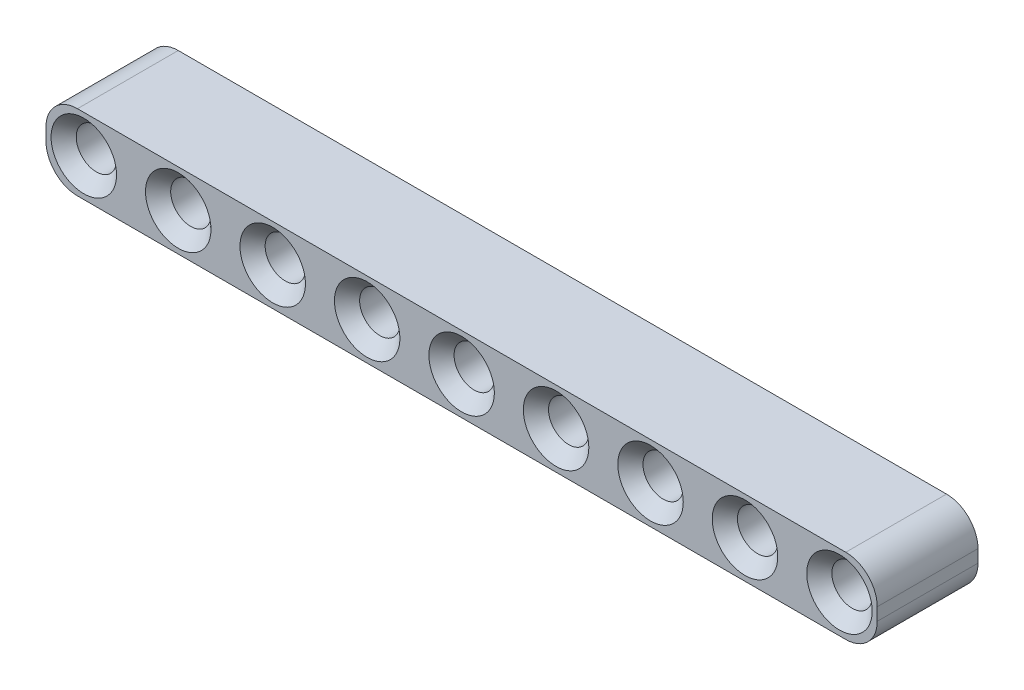
SolidWorks part; units mm, degrees
ref_plane "Front Plane" through (0, 0, 0) normal (0, 0, 1) x (1, 0, 0)
ref_plane "Top Plane" through (0, 0, 0) normal (0, 1, 0) x (1, 0, 0)
ref_plane "Right Plane" through (0, 0, 0) normal (1, 0, 0) x (0, 0, -1)
sketch "Sketch1" plane through (0, 0, 0) normal (0, 0, 1) x (1, 0, 0)
  line L1 (-0.5, 3) -> (60.5, 3)
  line L2 (-3, 0.5) -> (-3, -0.5)
  line L3 (-0.5, -3) -> (60.5, -3)
  line L4 (63, 0.5) -> (63, -0.5)
  circle A0 centre (0, 0) radius 1.6
  arc A1 (60.5, -3) -> (63, -0.5) centre (60.5, -0.5) ccw
  arc A2 (60.5, 3) -> (63, 0.5) centre (60.5, 0.5) cw
  arc A3 (-3, -0.5) -> (-0.5, -3) centre (-0.5, -0.5) ccw
  arc A4 (-0.5, 3) -> (-3, 0.5) centre (-0.5, 0.5) ccw
  circle A5 centre (7.5, 0) radius 1.6
  circle A6 centre (15, 0) radius 1.6
  circle A7 centre (22.5, 0) radius 1.6
  circle A8 centre (30, 0) radius 1.6
  circle A9 centre (37.5, 0) radius 1.6
  circle A10 centre (45, 0) radius 1.6
  circle A11 centre (52.5, 0) radius 1.6
  circle A12 centre (60, 0) radius 1.6
  point P8 (-3, 0)
  point P14 (-3, -3)
  point P17 (-3, 3)
  dimension "D1" = 3.2
  dimension "D4" = 2.5
  dimension "D2" = 6
  dimension "D3" = 3
  dimension "D6" = 7.5
  dimension "D5" = 9
extrude "Boss-Extrude1" add sketch "Sketch1" along normal blind 8
chamfer "Chamfer1" distance 1 angle 45 18 edges at (61.6, 0, 0) (61.6, 0, 8) (54.1, 0, 0) (54.1, 0, 8) (46.6, 0, 0) (46.6, 0, 8) (39.1, 0, 0) (39.1, 0, 8) (31.6, 0, 0) (31.6, 0, 8) (24.1, 0, 0) (24.1, 0, 8) (16.6, 0, 0) (16.6, 0, 8) (9.1, 0, 0) (9.1, 0, 8) (1.6, 0, 0) (1.6, 0, 8)
